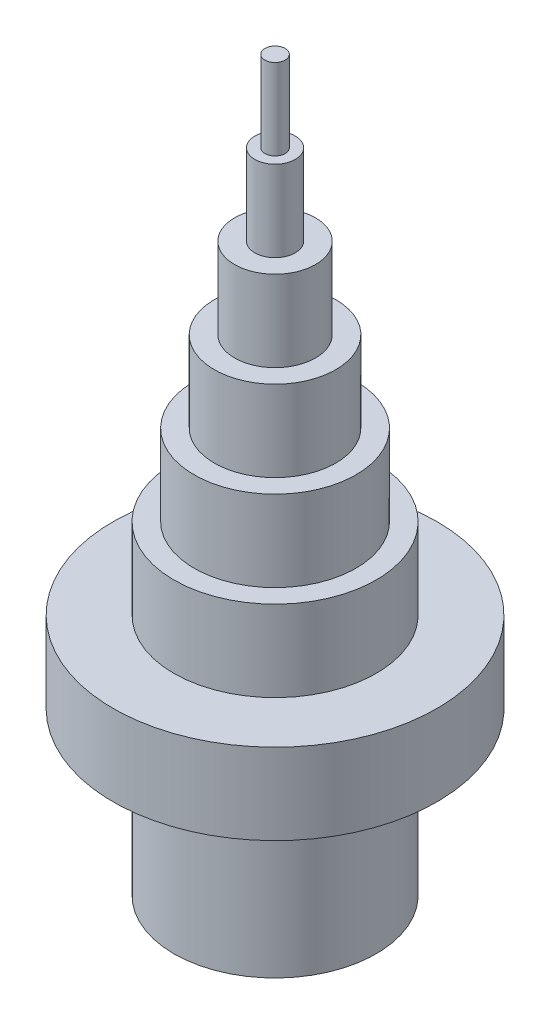
SolidWorks part; units mm, degrees
ref_plane "Front Plane" through (0, 0, 0) normal (0, 0, 1) x (1, 0, 0)
ref_plane "Top Plane" through (0, 0, 0) normal (0, 1, 0) x (1, 0, 0)
ref_plane "Right Plane" through (0, 0, 0) normal (1, 0, 0) x (0, 0, -1)
sketch "Sketch1" plane through (0, 0, 0) normal (0, 0, 1) x (1, 0, 0)
  line L0 (0, 0) -> (0, 70.5778) construction
  line L1 (0, 0) -> (25, 0)
  line L2 (25, 0) -> (25, 40)
  line L3 (25, 40) -> (40, 40)
  line L4 (40, 40) -> (40, 60)
  line L5 (40, 60) -> (25, 60)
  line L6 (25, 60) -> (25, 80)
  line L7 (25, 80) -> (20, 80)
  line L8 (20, 80) -> (20, 100)
  line L9 (20, 100) -> (15, 100)
  line L10 (15, 100) -> (15, 120)
  line L11 (15, 120) -> (10, 120)
  line L12 (10, 120) -> (10, 140)
  line L13 (10, 140) -> (5, 140)
  line L14 (5, 140) -> (5, 160)
  line L15 (5, 160) -> (2.5, 160)
  line L16 (2.5, 160) -> (2.5, 180)
  line L17 (2.5, 180) -> (0, 180)
  line L18 (0, 180) -> (0, 0)
  line L19 (0, 225.5193) -> (0, -41.8511) construction
  dimension "D1" = 40
  dimension "D2" = 20
  dimension "D3" = 20
  dimension "D4" = 180
  dimension "D5" = 20
  dimension "D6" = 20
  dimension "D7" = 20
  dimension "D8" = 20
  dimension "D9" = 20
  dimension "D10" = 5
  dimension "D11" = 10
  dimension "D12" = 20
  dimension "D13" = 30
  dimension "D14" = 40
  dimension "D15" = 50
  dimension "D16" = 80
  dimension "D17" = 50
revolve "Revolve1" add sketch "Sketch1" angle 360 about L0
sketch "Sketch2" plane through (0, 0, 0) normal (0, -1, 0) x (1, 0, 0)
  circle A0 centre (0, 0) radius 20
extrude "Cut-Extrude1" cut sketch "Sketch2" against normal blind 40
